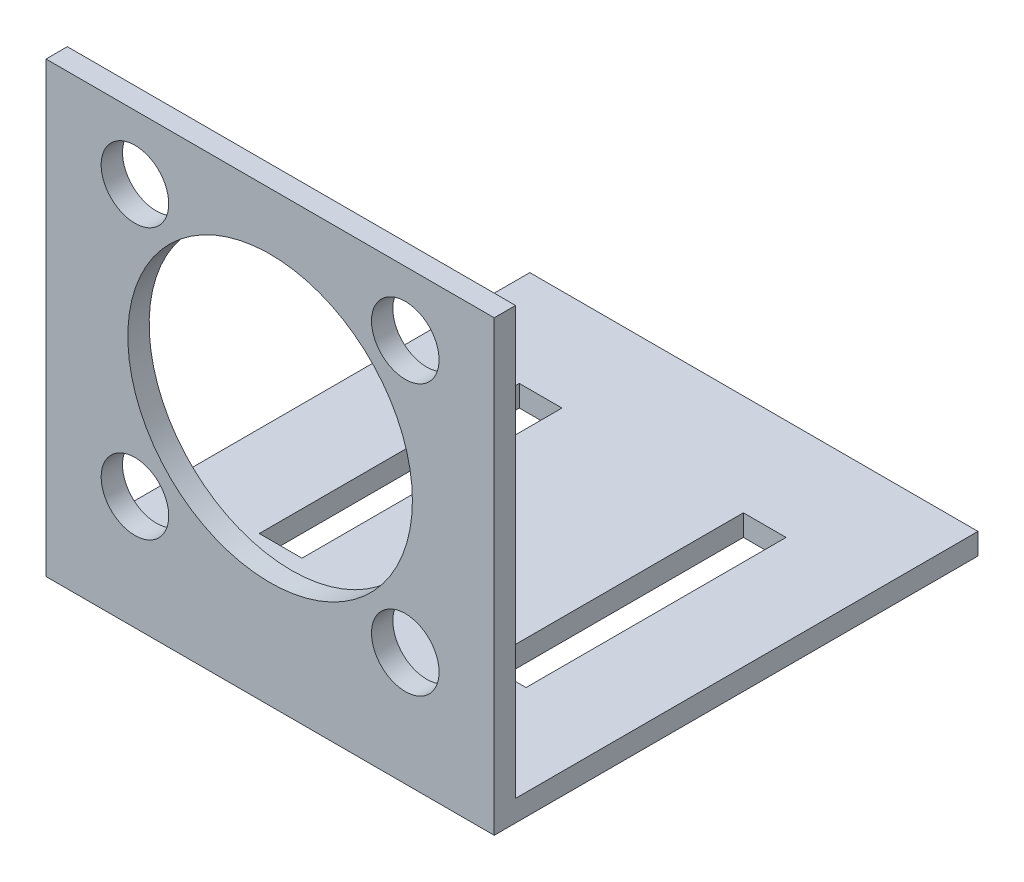
SolidWorks part; units mm, degrees
ref_plane "Front Plane" through (0, 0, 0) normal (0, 0, 1) x (1, 0, 0)
ref_plane "Top Plane" through (0, 0, 0) normal (0, 1, 0) x (1, 0, 0)
ref_plane "Right Plane" through (0, 0, 0) normal (1, 0, 0) x (0, 0, -1)
sketch "Sketch1" plane through (0, 0, 0) normal (1, 0, 0) x (0, 0, -1)
  line L0 (-31.8027, 29.4238) -> (-31.8027, -30.5762)
  line L1 (-31.8027, -30.5762) -> (33.1973, -30.5762)
  line L2 (33.1973, -30.5762) -> (33.1973, -33.5762)
  line L3 (33.1973, -33.5762) -> (-34.8027, -33.5762)
  line L4 (-34.8027, -33.5762) -> (-34.8027, 29.4238)
  line L5 (-34.8027, 29.4238) -> (-31.8027, 29.4238)
  dimension "D1" = 60
  dimension "D2" = 3
  dimension "D3" = 3
  dimension "D4" = 65
  dimension "D5" = 31.8027
  dimension "D6" = 30.5762
extrude "Boss-Extrude1" add sketch "Sketch1" along normal blind 63
sketch "Sketch2" plane through (0, 0, 0) normal (0, 0, 1) x (1, 0, 0)
  line L0 (63, -26.5762) -> (0, -26.5762) construction
  line L1 (63, -30.5762) -> (63, 29.4238) construction
  line L2 (0, -30.5762) -> (0, 29.4238) construction
  line L3 (63, -30.5762) -> (0, -30.5762) construction
  line L4 (31.5, 29.4238) -> (31.5, -26.5762) construction
  line L5 (63, 29.4238) -> (0, 29.4238) construction
  line L6 (60, 29.4238) -> (60, -26.5762) construction
  line L7 (60, 1.4238) -> (0, 1.4238) construction
  circle A0 centre (50.5, -17.5762) radius 4.75
  circle A1 centre (50.5, 20.4238) radius 4.75
  circle A2 centre (12.5, -17.5762) radius 4.75
  circle A3 centre (12.5, 20.4238) radius 4.75
  circle A4 centre (31.5, 1.4238) radius 20
  dimension "D3" = 9.5
  dimension "D6" = 40
  dimension "D1" = 4
  dimension "D2" = 3
  dimension "D4" = 19
  dimension "D5" = 19
extrude "Cut-Extrude1" cut sketch "Sketch2" against normal through all both and the other way through all
sketch "Sketch3" plane through (0, -30.5762, 0) normal (0, 1, 0) x (1, 0, 0)
  line L0 (31.5, 33.1973) -> (31.5, -31.8027) construction
  line L1 (63, 33.1973) -> (0, 33.1973) construction
  line L2 (63, -31.8027) -> (0, -31.8027) construction
  line L4 (12.75, 18.9726) -> (18.75, 18.9726)
  line L5 (12.75, 18.9726) -> (12.75, -17.578)
  line L6 (12.75, -17.578) -> (18.75, -17.578)
  line L7 (18.75, 18.9726) -> (18.75, -17.578)
  line L8 (50.25, -17.578) -> (44.25, -17.578)
  line L9 (44.25, 18.9726) -> (44.25, -17.578)
  line L10 (50.25, 18.9726) -> (44.25, 18.9726)
  line L11 (50.25, 18.9726) -> (50.25, -17.578)
  point P10 (15.75, -17.578)
  point P11 (18.75, 0.6973)
  dimension "D1" = 6
  dimension "D2" = 15.75
  dimension "D3" = 32.5
extrude "Cut-Extrude2" cut sketch "Sketch3" against normal through all
